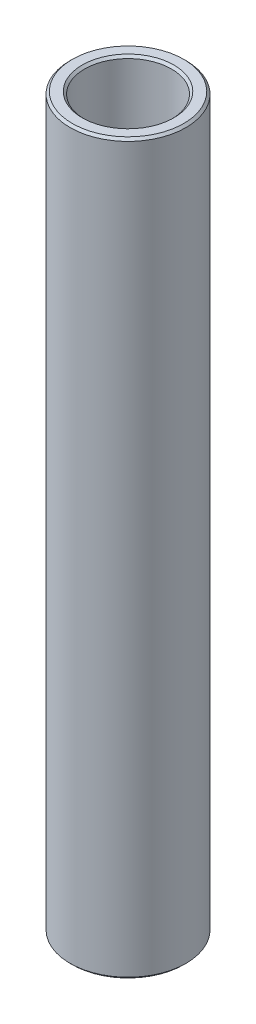
SolidWorks part; units mm, degrees
ref_plane "Front Plane" through (0, 0, 0) normal (0, 0, 1) x (1, 0, 0)
ref_plane "Top Plane" through (0, 0, 0) normal (0, 1, 0) x (1, 0, 0)
ref_plane "Right Plane" through (0, 0, 0) normal (1, 0, 0) x (0, 0, -1)
sketch "Sketch1" plane through (0, 0, 0) normal (0, 0, 1) x (1, 0, 0)
  line L0 (4.7625, 72.7024) -> (4.7625, 152.4742)
  line L1 (4.7625, 152.4742) -> (6.35, 152.4742)
  line L2 (6.35, 152.4742) -> (6.35, 72.7024)
  line L3 (6.35, 72.7024) -> (4.7625, 72.7024)
  line L4 (-10.0875, 78.6269) -> (-120.0875, 78.6269) construction
  line L6 (0, 63.1774) -> (0, 161.9992) construction
  dimension "D1" = 9.525
  dimension "D2" = 9.525
  dimension "D3" = 12.7
  dimension "D4" = 9.525
revolve "Revolve1" add sketch "Sketch1" angle 360 about L6
chamfer "Chamfer1" distance 0.254 angle 45 4 edges at (6.35, 152.4742, 0) (4.7625, 152.4742, 0) (4.7625, 72.7024, 0) (6.35, 72.7024, 0)
equation "\"D4@Sketch1\"=\"D1@Sketch1\""
